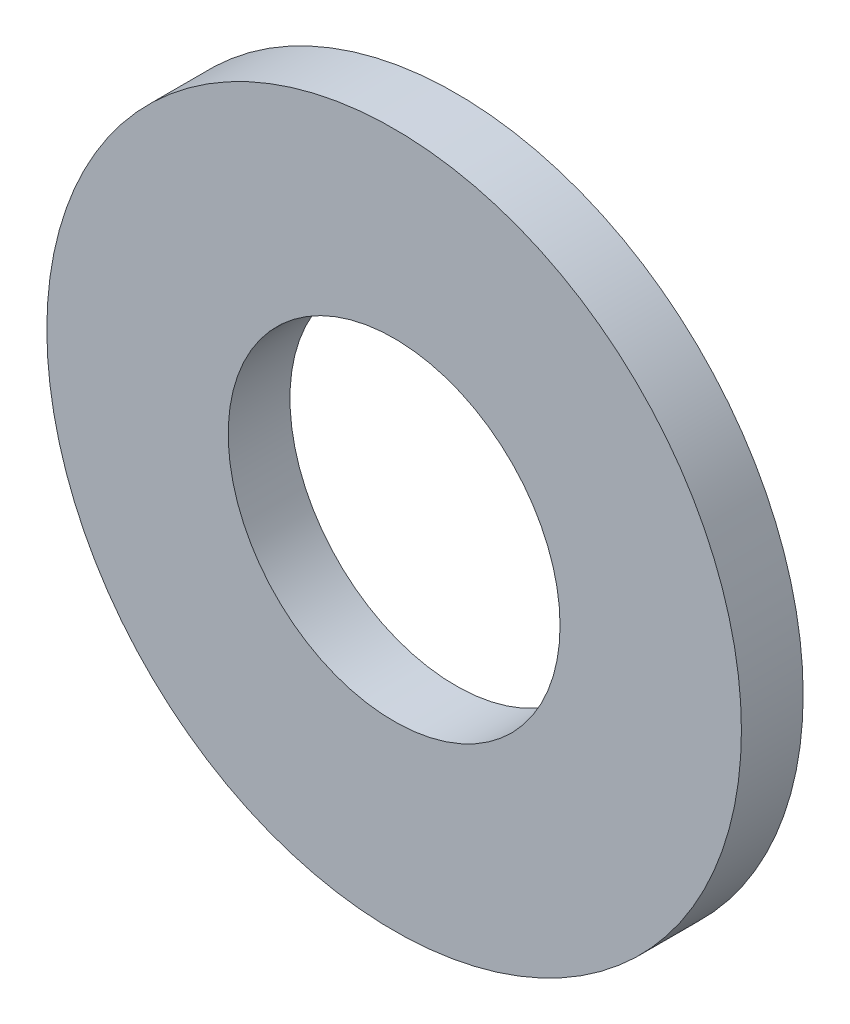
SolidWorks part; units mm, degrees
ref_plane "Front" through (0, 0, 0) normal (0, 0, 1) x (1, 0, 0)
ref_plane "Top" through (0, 0, 0) normal (0, 1, 0) x (1, 0, 0)
ref_plane "Right" through (0, 0, 0) normal (1, 0, 0) x (0, 0, -1)
sketch "Sketch1" plane through (0, 0, 0) normal (0, 0, 1) x (1, 0, 0)
  circle A0 centre (0, 0) radius 2.15
  circle A1 centre (0, 0) radius 4.5
  dimension "d1" = 4.3
  dimension "d2" = 9
extrude "Base-Extrude" add sketch "Sketch1" against normal blind 0.8
